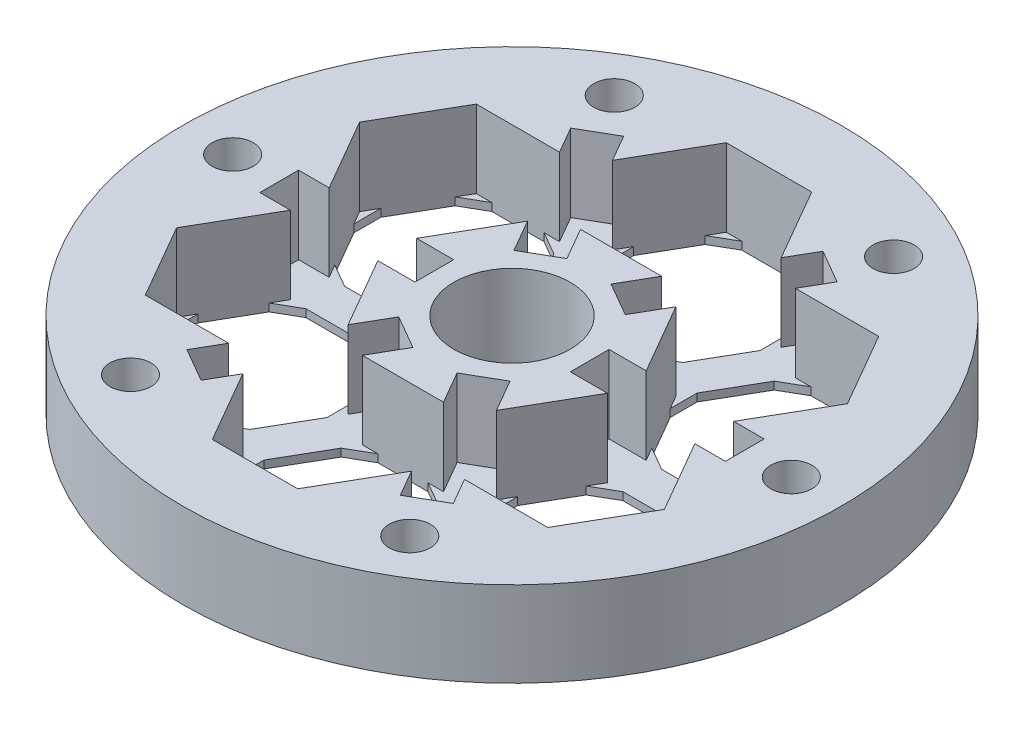
SolidWorks part; units mm, degrees
ref_plane "Front Plane" through (0, 0, 0) normal (0, 0, 1) x (1, 0, 0)
ref_plane "Top Plane" through (0, 0, 0) normal (0, 1, 0) x (1, 0, 0)
ref_plane "Right Plane" through (0, 0, 0) normal (1, 0, 0) x (0, 0, -1)
sketch "Sketch2" plane through (0, 0, 0) normal (0, 1, 0) x (1, 0, 0)
  circle A0 centre (0, 0) radius 42.5
  dimension "D1" = 85
extrude "Boss-Extrude1" add sketch "Sketch2" along normal blind 11
sketch "Sketch3" plane through (0, 11, 0) normal (0, 1, 0) x (1, 0, 0)
  line L60 (0, 33.1406) -> (0, 0) construction
  line L61 (8.2583, 18.8368) -> (11.0111, 23.6047) construction
  line L62 (10.8763, 23.8382) -> (5.5055, 33.1406)
  line L63 (5.5055, 33.1406) -> (-5.5055, 33.1406)
  line L64 (-5.5055, 33.1406) -> (-10.8763, 23.8382)
  line L65 (-11.0111, 23.6047) -> (-8.2583, 18.8368) construction
  line L66 (-5.2359, 14.0688) -> (5.2359, 14.0688)
  line L67 (0, 0) -> (5.0107, 8.6789) construction
  line L68 (2.8457, 9.9289) -> (5.2359, 14.0688)
  line L69 (12.8457, 27.2494) -> (17.1758, 24.7494)
  line L70 (17.1758, 24.7494) -> (15.2064, 21.3382)
  line L71 (7.1758, 7.4289) -> (2.8457, 9.9289)
  line L72 (14.9367, 2.2665) -> (25.9478, 2.2665) construction
  line L73 (26.0827, 2.5) -> (31.4534, 11.8024)
  line L74 (31.4534, 11.8024) -> (25.9478, 21.3382)
  line L75 (25.9478, 21.3382) -> (15.2064, 21.3382)
  line L76 (14.9367, 21.3382) -> (9.4312, 11.8024) construction
  line L77 (9.566, 11.5688) -> (14.8019, 2.5)
  line L78 (10.0215, -2.5) -> (10.0215, 2.5)
  line L79 (10.0215, 2.5) -> (14.8019, 2.5)
  line L80 (30.0215, 2.5) -> (30.0215, -2.5)
  line L81 (30.0215, -2.5) -> (26.0827, -2.5)
  line L82 (9.4312, -11.8024) -> (14.9367, -21.3382) construction
  line L83 (15.2064, -21.3382) -> (25.9478, -21.3382)
  line L84 (25.9478, -21.3382) -> (31.4534, -11.8024)
  line L85 (31.4534, -11.8024) -> (26.0827, -2.5)
  line L86 (25.9478, -2.2665) -> (14.9367, -2.2665) construction
  line L87 (14.8019, -2.5) -> (9.566, -11.5688)
  line L88 (2.8457, -9.9289) -> (7.1758, -7.4289)
  line L89 (7.1758, -7.4289) -> (9.566, -11.5688)
  line L90 (17.1758, -24.7494) -> (12.8457, -27.2494)
  line L91 (12.8457, -27.2494) -> (10.8763, -23.8382)
  line L92 (-5.5055, -14.0688) -> (-11.0111, -23.6047) construction
  line L93 (-10.8763, -23.8382) -> (-5.5055, -33.1406)
  line L94 (-5.5055, -33.1406) -> (5.5055, -33.1406)
  line L95 (5.5055, -33.1406) -> (10.8763, -23.8382)
  line L96 (11.0111, -23.6047) -> (5.5055, -14.0688) construction
  line L97 (5.2359, -14.0688) -> (-5.2359, -14.0688)
  line L98 (-7.1758, -7.4289) -> (-2.8457, -9.9289)
  line L99 (-2.8457, -9.9289) -> (-5.2359, -14.0688)
  line L100 (-12.8457, -27.2494) -> (-17.1758, -24.7494)
  line L101 (-17.1758, -24.7494) -> (-15.2064, -21.3382)
  line L102 (-14.9367, -2.2665) -> (-25.9478, -2.2665) construction
  line L103 (-26.0827, -2.5) -> (-31.4534, -11.8024)
  line L104 (-31.4534, -11.8024) -> (-25.9478, -21.3382)
  line L105 (-25.9478, -21.3382) -> (-15.2064, -21.3382)
  line L106 (-14.9367, -21.3382) -> (-9.4312, -11.8024) construction
  line L107 (-9.566, -11.5688) -> (-14.8019, -2.5)
  line L108 (-10.0215, 2.5) -> (-10.0215, -2.5)
  line L109 (-10.0215, -2.5) -> (-14.8019, -2.5)
  line L110 (-30.0215, -2.5) -> (-30.0215, 2.5)
  line L111 (-30.0215, 2.5) -> (-26.0827, 2.5)
  line L112 (-9.4312, 11.8024) -> (-14.9367, 21.3382) construction
  line L113 (-15.2064, 21.3382) -> (-25.9478, 21.3382)
  line L114 (-25.9478, 21.3382) -> (-31.4534, 11.8024)
  line L115 (-31.4534, 11.8024) -> (-26.0827, 2.5)
  line L116 (-25.9478, 2.2665) -> (-14.9367, 2.2665) construction
  line L117 (-14.8019, 2.5) -> (-9.566, 11.5688)
  line L118 (-2.8457, 9.9289) -> (-7.1758, 7.4289)
  line L119 (-7.1758, 7.4289) -> (-9.566, 11.5688)
  line L120 (-17.1758, 24.7494) -> (-12.8457, 27.2494)
  line L121 (-12.8457, 27.2494) -> (-10.8763, 23.8382)
  line L122 (-9.566, 11.5688) -> (-15.2064, 21.3382) construction
  line L123 (-15.2064, 21.3382) -> (-17.1758, 24.7494)
  line L124 (-8.2583, 18.8368) -> (-5.5055, 14.0688) construction
  line L125 (-9.1048, 20.77) -> (-7.0073, 17.1371) construction
  line L126 (-5.2359, 14.0688) -> (-2.8457, 9.9289)
  line L127 (-10.8763, 23.8382) -> (-9.1048, 20.77) construction
  line L128 (-7.0073, 17.1371) -> (-5.2359, 14.0688) construction
  line L129 (7.0073, 17.1371) -> (9.1048, 20.77) construction
  line L130 (10.8763, 23.8382) -> (12.8457, 27.2494)
  line L131 (5.5055, 14.0688) -> (8.2583, 18.8368) construction
  line L132 (5.0107, 8.6789) -> (15.0107, 25.9994) construction
  line L133 (15.2064, 21.3382) -> (9.566, 11.5688) construction
  line L134 (9.566, 11.5688) -> (7.1758, 7.4289)
  line L135 (9.1048, 20.77) -> (10.8763, 23.8382) construction
  line L136 (5.2359, 14.0688) -> (7.0073, 17.1371) construction
  line L137 (9.4312, 11.8024) -> (9.566, 11.5688) construction
  line L138 (5.2359, 14.0688) -> (5.5055, 14.0688) construction
  line L139 (15.2064, 21.3382) -> (14.9367, 21.3382) construction
  line L140 (11.0111, 23.6047) -> (10.8763, 23.8382) construction
  line L141 (-14.9367, 21.3382) -> (-15.2064, 21.3382) construction
  line L142 (-10.8763, 23.8382) -> (-11.0111, 23.6047) construction
  line L143 (-9.566, 11.5688) -> (-9.4312, 11.8024) construction
  line L144 (-5.5055, 14.0688) -> (-5.2359, 14.0688) construction
  line L145 (-26.0827, 2.5) -> (-14.8019, 2.5) construction
  line L146 (-14.8019, 2.5) -> (-10.0215, 2.5)
  line L147 (-14.8019, -2.5) -> (-26.0827, -2.5) construction
  line L148 (-26.0827, -2.5) -> (-30.0215, -2.5)
  line L149 (-15.2064, -21.3382) -> (-9.566, -11.5688) construction
  line L150 (-9.566, -11.5688) -> (-7.1758, -7.4289)
  line L151 (-5.2359, -14.0688) -> (-10.8763, -23.8382) construction
  line L152 (-10.8763, -23.8382) -> (-12.8457, -27.2494)
  line L153 (10.8763, -23.8382) -> (5.2359, -14.0688) construction
  line L154 (5.2359, -14.0688) -> (2.8457, -9.9289)
  line L155 (9.566, -11.5688) -> (15.2064, -21.3382) construction
  line L156 (15.2064, -21.3382) -> (17.1758, -24.7494)
  line L157 (26.0827, -2.5) -> (14.8019, -2.5) construction
  line L158 (14.8019, -2.5) -> (10.0215, -2.5)
  line L159 (14.8019, 2.5) -> (26.0827, 2.5) construction
  line L160 (26.0827, 2.5) -> (30.0215, 2.5)
  line L161 (-26.0827, 2.5) -> (-25.9478, 2.2665) construction
  line L162 (-25.9478, -2.2665) -> (-26.0827, -2.5) construction
  line L163 (-14.9367, 2.2665) -> (-14.8019, 2.5) construction
  line L164 (-14.8019, -2.5) -> (-14.9367, -2.2665) construction
  line L165 (-9.4312, -11.8024) -> (-9.566, -11.5688) construction
  line L166 (-5.2359, -14.0688) -> (-5.5055, -14.0688) construction
  line L167 (-15.2064, -21.3382) -> (-14.9367, -21.3382) construction
  line L168 (-11.0111, -23.6047) -> (-10.8763, -23.8382) construction
  line L169 (10.8763, -23.8382) -> (11.0111, -23.6047) construction
  line L170 (14.9367, -21.3382) -> (15.2064, -21.3382) construction
  line L171 (5.5055, -14.0688) -> (5.2359, -14.0688) construction
  line L172 (9.566, -11.5688) -> (9.4312, -11.8024) construction
  line L173 (14.9367, -2.2665) -> (14.8019, -2.5) construction
  line L174 (26.0827, -2.5) -> (25.9478, -2.2665) construction
  line L175 (25.9478, 2.2665) -> (26.0827, 2.5) construction
  line L176 (14.8019, 2.5) -> (14.9367, 2.2665) construction
  line L177 (0, 0) -> (-4.5964, 0) construction
  line L178 (-4.5964, 0) -> (-4.5964, 23.6047) construction
  line L179 (-4.5964, 23.6047) -> (0, 23.6047) construction
  arc A1 (0, 14.0688) -> (7.0073, 17.1371) centre (0, 23.6047) ccw construction
  arc A2 (-8.2583, 18.8368) -> (-7.0073, 17.1371) centre (0, 23.6047) ccw construction
  arc A3 (-8.2583, 28.3727) -> (-9.1048, 20.77) centre (0, 23.6047) ccw construction
  arc A4 (-9.1048, 20.77) -> (-8.2583, 18.8368) centre (0, 23.6047) ccw construction
  arc A5 (-7.0073, 17.1371) -> (0, 14.0688) centre (0, 23.6047) ccw construction
  arc A6 (7.0073, 17.1371) -> (8.2583, 18.8368) centre (0, 23.6047) ccw construction
  arc A7 (8.2583, 18.8368) -> (9.1048, 20.77) centre (0, 23.6047) ccw construction
  arc A8 (9.1048, 20.77) -> (8.2583, 28.3727) centre (0, 23.6047) ccw construction
  arc A9 (8.2583, 28.3727) -> (-8.2583, 28.3727) centre (0, 23.6047) ccw construction
  point P16 (15.0107, 25.9994)
  point P69 (0, 0)
  dimension "D2" = 19.0718
  dimension "D1" = 33.1406
  dimension "D3" = 5
  dimension "D4" = 30.0215
  dimension "D5" = 20
  dimension "D6" = 30
  dimension "D7" = 6
extrude "Cut-Extrude3" cut sketch "Sketch3" against normal blind 11
sketch "Sketch4" plane through (0, 11, 0) normal (0, 1, 0) x (1, 0, 0)
  line L0 (0, 0) -> (18.0107, 31.1955) construction
  line L2 (17.1758, 24.7494) -> (12.8457, 27.2494) construction
  circle A1 centre (18.0107, 31.1955) radius 2.65
  circle A2 centre (36.0215, 0) radius 2.65
  circle A3 centre (18.0107, -31.1955) radius 2.65
  circle A4 centre (-18.0107, -31.1955) radius 2.65
  circle A5 centre (-36.0215, 0) radius 2.65
  circle A6 centre (-18.0107, 31.1955) radius 2.65
  point P5 (15.0107, 25.9994)
  point P20 (0, 0)
  dimension "D2" = 6
  dimension "D1" = 5.3
  dimension "D3" = 6
extrude "Cut-Extrude4" cut sketch "Sketch4" against normal through all
sketch "Sketch7" plane through (0, 0, 0) normal (0, -1, 0) x (1, 0, 0)
  line L0 (-7.1758, 7.4289) -> (-2.8457, 9.9289)
  line L1 (-2.8457, 9.9289) -> (-12.8457, 27.2494)
  line L2 (-12.8457, 27.2494) -> (-17.1758, 24.7494)
  line L3 (-17.1758, 24.7494) -> (-7.1758, 7.4289)
  line L4 (12.8457, 27.2494) -> (2.8457, 9.9289)
  line L5 (2.8457, 9.9289) -> (7.1758, 7.4289)
  line L6 (7.1758, 7.4289) -> (17.1758, 24.7494)
  line L7 (17.1758, 24.7494) -> (12.8457, 27.2494)
  line L8 (30.0215, 2.5) -> (10.0215, 2.5)
  line L9 (10.0215, 2.5) -> (10.0215, -2.5)
  line L10 (10.0215, -2.5) -> (30.0215, -2.5)
  line L11 (30.0215, -2.5) -> (30.0215, 2.5)
  line L12 (17.1758, -24.7494) -> (7.1758, -7.4289)
  line L13 (7.1758, -7.4289) -> (2.8457, -9.9289)
  line L14 (2.8457, -9.9289) -> (12.8457, -27.2494)
  line L15 (12.8457, -27.2494) -> (17.1758, -24.7494)
  line L16 (-12.8457, -27.2494) -> (-2.8457, -9.9289)
  line L17 (-2.8457, -9.9289) -> (-7.1758, -7.4289)
  line L18 (-7.1758, -7.4289) -> (-17.1758, -24.7494)
  line L19 (-17.1758, -24.7494) -> (-12.8457, -27.2494)
  line L20 (-30.0215, -2.5) -> (-10.0215, -2.5)
  line L21 (-10.0215, -2.5) -> (-10.0215, 2.5)
  line L22 (-10.0215, 2.5) -> (-30.0215, 2.5)
  line L23 (-30.0215, 2.5) -> (-30.0215, -2.5)
  point P31 (0, 0)
  dimension "D1" = 6
extrude "Boss-Extrude2" add sketch "Sketch7" against normal blind 1
sketch "Sketch6" plane through (0, 0, 0) normal (0, 1, 0) x (1, 0, 0)
  circle A0 centre (18.0107, 31.1955) radius 4.4
  circle A1 centre (36.0215, 0) radius 4.4
  circle A2 centre (18.0107, -31.1955) radius 4.4
  circle A3 centre (-18.0107, -31.1955) radius 4.4
  circle A4 centre (-36.0215, 0) radius 4.4
  circle A5 centre (-18.0107, 31.1955) radius 4.4
  point P16 (0, 0)
  dimension "D1" = 8.8
  dimension "D2" = 6
extrude "Cut-Extrude6" cut sketch "Sketch6" along normal blind 5.4
sketch "Sketch8" plane through (0, 11, 0) normal (0, 1, 0) x (1, 0, 0)
  circle A0 centre (0, 0) radius 7.5
  dimension "D1" = 15
extrude "Cut-Extrude7" cut sketch "Sketch8" against normal through all and the other way through all
sketch "Sketch11" plane through (0, 0, 0) normal (0, -1, 0) x (1, 0, 0)
  line L0 (17.2064, 21.3382) -> (14.2064, 19.6062)
  line L1 (15.2064, 21.3382) -> (25.9478, 21.3382) construction
  line L2 (9.566, 11.5688) -> (15.2064, 21.3382) construction
  line L3 (14.2064, 19.6062) -> (15.2064, 21.3382)
  line L4 (15.2064, 21.3382) -> (17.2064, 21.3382)
  line L5 (25.9478, 21.3382) -> (26.9478, 19.6062)
  line L6 (25.9478, 21.3382) -> (31.4534, 11.8024) construction
  line L7 (26.9478, 19.6062) -> (23.9478, 21.3382)
  line L8 (23.9478, 21.3382) -> (25.9478, 21.3382)
  line L9 (30.4534, 10.0703) -> (31.4534, 11.8024)
  line L10 (31.4534, 11.8024) -> (26.0827, 2.5) construction
  line L11 (31.4534, 11.8024) -> (30.4534, 13.5344)
  line L12 (30.4534, 13.5344) -> (30.4534, 10.0703)
  line L13 (24.0827, 2.5) -> (27.0827, 4.2321)
  line L14 (26.0827, 2.5) -> (14.8019, 2.5) construction
  line L15 (27.0827, 4.2321) -> (26.0827, 2.5)
  line L16 (26.0827, 2.5) -> (24.0827, 2.5)
  line L17 (13.8019, 4.2321) -> (14.8019, 2.5)
  line L18 (9.566, 11.5688) -> (14.8019, 2.5) construction
  line L19 (14.8019, 2.5) -> (16.8019, 2.5)
  line L20 (16.8019, 2.5) -> (13.8019, 4.2321)
  line L21 (10.566, 9.8368) -> (9.566, 11.5688)
  line L22 (9.566, 11.5688) -> (10.566, 13.3009)
  line L23 (10.566, 13.3009) -> (10.566, 9.8368)
  dimension "D1" = 1
  dimension "D2" = 1
  dimension "D3" = 1
  dimension "D4" = 1
  dimension "D5" = 1
  dimension "D6" = 1
extrude "Boss-Extrude3" add sketch "Sketch11" against normal up to surface (1 mm away) up to face at (20.2319, 1, 0)
pattern_circular "CirPattern1" count 6 over 360 about axis through (0, 0, 0) along (0, 1, 0) of "Boss-Extrude3"
